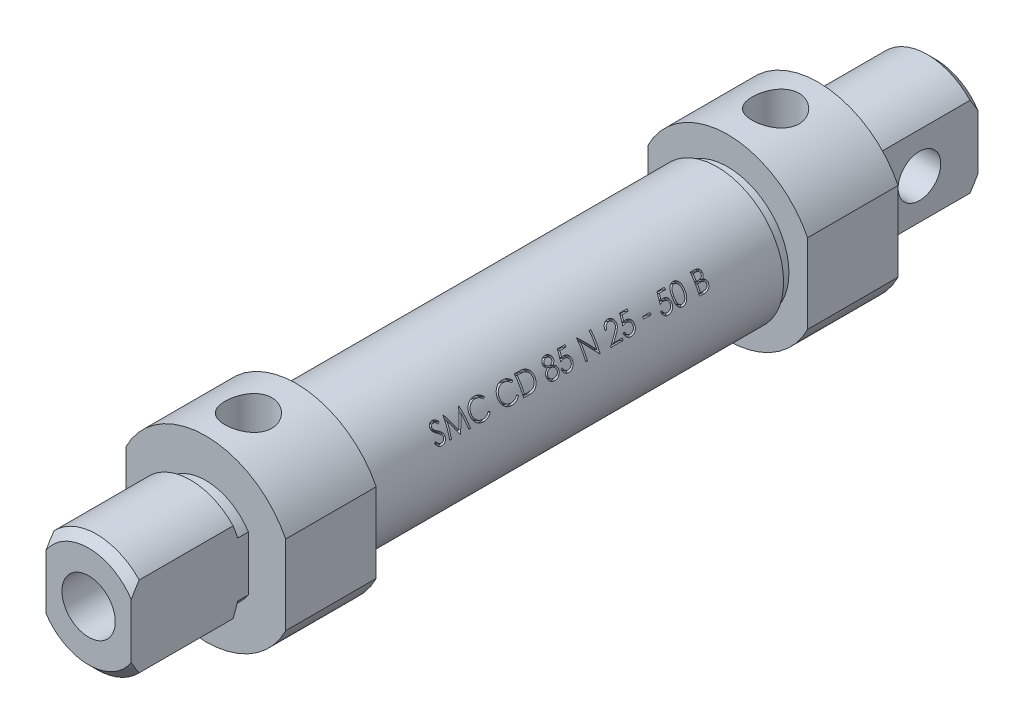
SolidWorks part; units mm, degrees
material "Acciaio in lega"
ref_plane "Piano frontale" through (0, 0, 0) normal (0, 0, 1) x (1, 0, 0)
ref_plane "Piano superiore" through (0, 0, 0) normal (0, 1, 0) x (1, 0, 0)
ref_plane "Piano destro" through (0, 0, 0) normal (1, 0, 0) x (0, 0, -1)
ref_axis "Assi1" through (0, 0, 10.7554) along (0, 0, -1)
sketch "Schizzo1" plane through (0, 0, 0) normal (1, 0, 0) x (0, 0, -1)
  line L0 (0, 0) -> (0, 5) construction
  line L1 (0, 11) -> (0, 5)
  line L2 (0, 0) -> (-6, 0) construction
  line L3 (0, 5) -> (25, 5)
  line L4 (0, 11) -> (22, 11)
  line L5 (-6, 0) -> (-28, 0) construction
  line L6 (22, 11) -> (22, 16.75)
  line L7 (22, 16.75) -> (39, 16.75)
  line L8 (39, 16.75) -> (39, 12.5)
  line L9 (39, 12.5) -> (120, 12.5)
  line L10 (120, 12.5) -> (120, 16.75)
  line L11 (120, 16.75) -> (137, 16.75)
  line L12 (137, 16.75) -> (137, 11)
  line L13 (137, 11) -> (159, 11)
  line L14 (159, 11) -> (159, 5)
  line L15 (30, 16.75) -> (30, 5.25) construction
  line L16 (129, 16.75) -> (129, 5.25) construction
  line L17 (22, 11) -> (30, 11) construction
  line L18 (137, 11) -> (129, 11) construction
  line L19 (0, 0) -> (79.5, 0) construction
  line L20 (79.5, 0) -> (79.5, 12.5) construction
  line L21 (25, 5) -> (25, 9.5)
  line L22 (25, 9.5) -> (134, 9.5)
  line L23 (134, 9.5) -> (134, 5)
  line L24 (134, 5) -> (159, 5)
  point P18 (25, 7.25)
  point P29 (137, 13.875)
  dimension "D1" = 10
  dimension "D2" = 22
  dimension "D3" = 22
  dimension "D4" = 33.5
  dimension "D5" = 17
  dimension "D6" = 115
  dimension "D7" = 22
  dimension "D8" = 22
  dimension "D9" = 25
  dimension "D10" = 28
  dimension "D11" = 22
  dimension "D12" = 8
  dimension "D13" = 3
  dimension "D14" = 3
  dimension "D15" = 3
revolve "Rivoluzione1" add sketch "Schizzo1" angle 360 about L2
sketch "Schizzo2" plane through (0, 0, 0) normal (1, 0, 0) x (0, 0, -1)
  line L0 (22, 9.5) -> (137, 9.5) construction
  line L1 (19.134, 11) -> (22, 11)
  line L2 (19.134, 11) -> (20, 9.5)
  line L3 (20, 9.5) -> (22, 9.5)
  line L4 (22, 11) -> (22, 9.5)
  line L5 (39, 12.5) -> (41, 12.5)
  line L6 (39, 12.5) -> (39, 11.5)
  line L7 (39, 11.5) -> (41, 11.5)
  line L8 (41, 12.5) -> (41, 11.5)
  line L9 (118, 12.5) -> (120, 12.5)
  line L10 (118, 12.5) -> (118, 11.5)
  line L11 (118, 11.5) -> (120, 11.5)
  line L12 (120, 12.5) -> (120, 11.5)
  line L13 (137, 16.75) -> (137, 11) construction
  line L14 (79.5, 9.5) -> (79.5, 0) construction
  dimension "D1" = 2
  dimension "D2" = 1
  dimension "D3" = 120
  dimension "D4" = 2
  dimension "D5" = 1.5
revolve "Taglia-Rivoluzione1" cut sketch "Schizzo2" angle 360 about axis through (0, 0, 10.7554) along (0, 0, -1)
chamfer "Smusso1" distance 1.5 angle 45 1 edges at (-11, 0, 0)
chamfer "Smusso2" distance 1.5 angle 45 1 edges at (-11, 0, -159)
sketch "Schizzo3" plane through (0, 0, 0) normal (0, 0, 1) x (1, 0, 0)
  line L0 (0, 0) -> (16.75, 0) construction
  line L1 (15, 16.75) -> (16.75, 16.75)
  line L2 (15, 16.75) -> (15, -16.75)
  line L3 (15, -16.75) -> (16.75, -16.75)
  line L4 (16.75, 16.75) -> (16.75, -16.75)
  line L5 (0, 16.75) -> (0, 0) construction
  line L6 (-16.75, 16.75) -> (-16.75, -16.75)
  line L7 (-15, -16.75) -> (-16.75, -16.75)
  line L8 (-15, 16.75) -> (-15, -16.75)
  line L9 (-15, 16.75) -> (-16.75, 16.75)
  dimension "D1" = 30
extrude "Taglio-Estrusione1" cut sketch "Schizzo3" against normal through all
sketch "Schizzo4" plane through (0, 0, 0) normal (0, 0, 1) x (1, 0, 0)
  line L0 (0, 16.75) -> (0, 0) construction
  line L1 (8, 16.75) -> (16.75, 16.75)
  line L2 (8, 16.75) -> (8, -16.75)
  line L3 (8, -16.75) -> (16.75, -16.75)
  line L4 (16.75, 16.75) -> (16.75, -16.75)
  line L5 (-16.75, 16.75) -> (-16.75, -16.75)
  line L6 (-8, -16.75) -> (-16.75, -16.75)
  line L7 (-8, 16.75) -> (-8, -16.75)
  line L8 (-8, 16.75) -> (-16.75, 16.75)
  dimension "D1" = 16
extrude "Taglio-Estrusione2" cut sketch "Schizzo4" against normal up to vertex (22 mm away) up to point (0, 11, -22)
ref_plane "Piano1" through (0, 0, -79.5) normal (0, 0, 1) x (1, 0, 0)
mirror "Specchia1" about plane through (0, 0, -79.5) normal (0, 0, 1) of "Taglio-Estrusione2"
sketch "Schizzo6" plane through (0, 0, 0) normal (1, 0, 0) x (0, 0, -1)
  line L0 (137, 16.75) -> (137, 11) construction
  line L1 (159, 5) -> (137, 5)
  line L2 (159, 5) -> (159, 0)
  line L3 (159, 0) -> (137, 0)
  line L4 (137, 5) -> (137, 0)
revolve "Rivoluzione2" add sketch "Schizzo6" angle 360 about L3
sketch "Schizzo5" plane through (0, 0, 0) normal (1, 0, 0) x (0, 0, -1)
  line L0 (148, 0) -> (-6, 0) construction
  line L1 (120, 12.5) -> (120, 16.75) construction
  circle A0 centre (148, 0) radius 4
  dimension "D1" = 8
  dimension "D2" = 154
  dimension "D3" = 28
extrude "Taglio-Estrusione3" cut sketch "Schizzo5" against normal through all and the other way through all
hole_wizard "Foro filettato G1/8-1" positions "Schizzo7" profile "Schizzo8" tap size "G1/8" standard "ISO"
sketch "Schizzo7" plane through (0, 0, 0) normal (0, 1, 0) x (1, 0, 0)
  line L0 (0, 0) -> (0, 25) construction
  point P0 (0, 30)
  point P4 (0, 129)
sketch "Schizzo8" plane through (0, 0, -30) normal (1, 0, 0) x (0, 0, -1)
  line L0 (0, 0) -> (0, 16.75)
  line L1 (0, 16.75) -> (4.4, 16.75)
  line L2 (4.4, 16.75) -> (4.4, 0)
  line L5 (4.4, 0) -> (0, 0)
  line L11 (0, -6.35) -> (0, 107.95) construction
  dimension "Thru Tap Drill Dia." = 8.8
  dimension "Thru Tap Drill Depth" = 16.75
cosmetic thread "Filettatura del foro1" parameters "D2"=9.728
cosmetic thread "Filettatura del foro2" parameters "D2"=9.728
ref_plane "Piano2" through (10.8253, 6.25, 0) normal (0.866, 0.5, 0) x (0, 0, -1)
sketch "Schizzo9" plane through (10.8253, 6.25, 0) normal (0.866, 0.5, 0) x (0, 0, -1)
  line L0 (50.0249, -1.75) -> (108.9751, -1.75) construction
  line L2 (79.5, -1.75) -> (79.5, 1.75) construction
  line L3 (79.5, 0) -> (79.5, 10.8253) construction
  text T0 "SMC CD 85 N 25 - 50 B"
  point P8 (79.5, 0)
  dimension "D1" = 3.5
extrude "Taglio-Estrusione4" cut sketch "Schizzo9" against normal blind 1
ref_plane "Piano3" through (0, 0, 6) normal (0, 0, 1) x (1, 0, 0)
